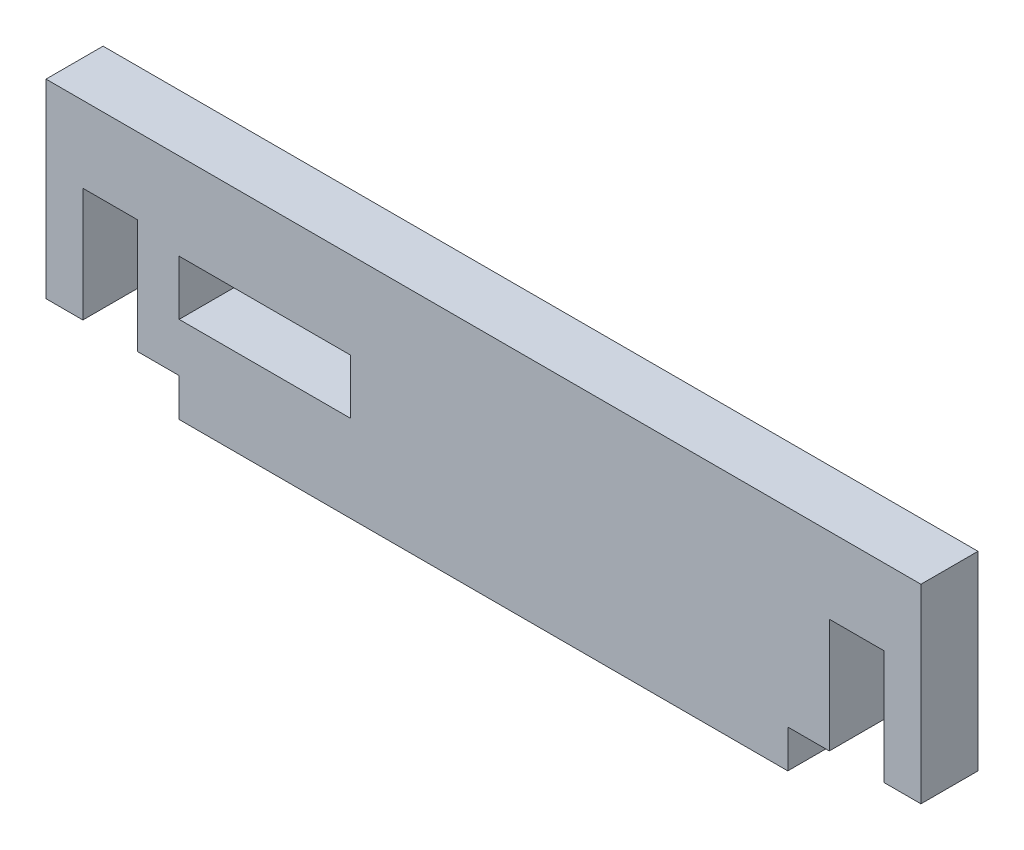
SolidWorks part; units mm, degrees
material "Arce"
ref_plane "Alzado" through (0, 0, 0) normal (0, 0, 1) x (1, 0, 0)
ref_plane "Planta" through (0, 0, 0) normal (0, 1, 0) x (1, 0, 0)
ref_plane "Vista lateral" through (0, 0, 0) normal (1, 0, 0) x (0, 0, -1)
sketch "Croquis1" plane through (0, 0, 0) normal (0, 0, 1) x (1, 0, 0)
  line L4 (16, 0) -> (16, 12) construction
  line L9 (0, 0) -> (32, 0)
  line L10 (0, 0) -> (0, 12)
  line L11 (0, 12) -> (32, 12)
  line L12 (32, 0) -> (32, 12)
  line L13 (0, 7.437) -> (9, 7.437)
  line L14 (0, 7.437) -> (0, 4.56)
  line L15 (0, 4.56) -> (9, 4.56)
  line L16 (9, 7.437) -> (9, 4.56)
  line L17 (32, 10) -> (39, 10)
  line L18 (32, 10) -> (32, 2)
  line L19 (32, 2) -> (39, 2)
  line L20 (39, 10) -> (39, 2)
  line L21 (0, 2) -> (-7, 2)
  line L22 (-7, 10) -> (-7, 2)
  line L23 (0, 10) -> (-7, 10)
  line L24 (34.1845, 2) -> (34.1845, 8)
  line L25 (34.1845, 8) -> (37.0615, 8)
  line L26 (37.0615, 8) -> (37.0615, 2)
  line L27 (32, 12) -> (39, 12)
  line L28 (39, 12) -> (39, 10)
  line L29 (-7, 12) -> (-7, 10)
  line L30 (0, 12) -> (-7, 12)
  line L31 (-5.0615, 8) -> (-5.0615, 2)
  line L32 (-2.1845, 2) -> (-2.1845, 8)
  line L33 (-2.1845, 8) -> (-5.0615, 8)
  dimension "D1" = 2.877
  dimension "D2" = 9
  dimension "D3" = 32
  dimension "D4" = 8
  dimension "D5" = 7
  dimension "D6" = 12
  dimension "D7" = 4.56
  dimension "D8" = 2
  dimension "D9" = 2.877
  dimension "D10" = 1.9385
  dimension "D11" = 6
extrude "Saliente-Extruir1" add sketch "Croquis1" along normal blind 3
equation "\"mdf_wid\"= 3mm"
equation "\"mdf_hei\"= 15mm"
equation "\"alturagato\"= 110mm"
equation "\"separacion\"= 13mm"
